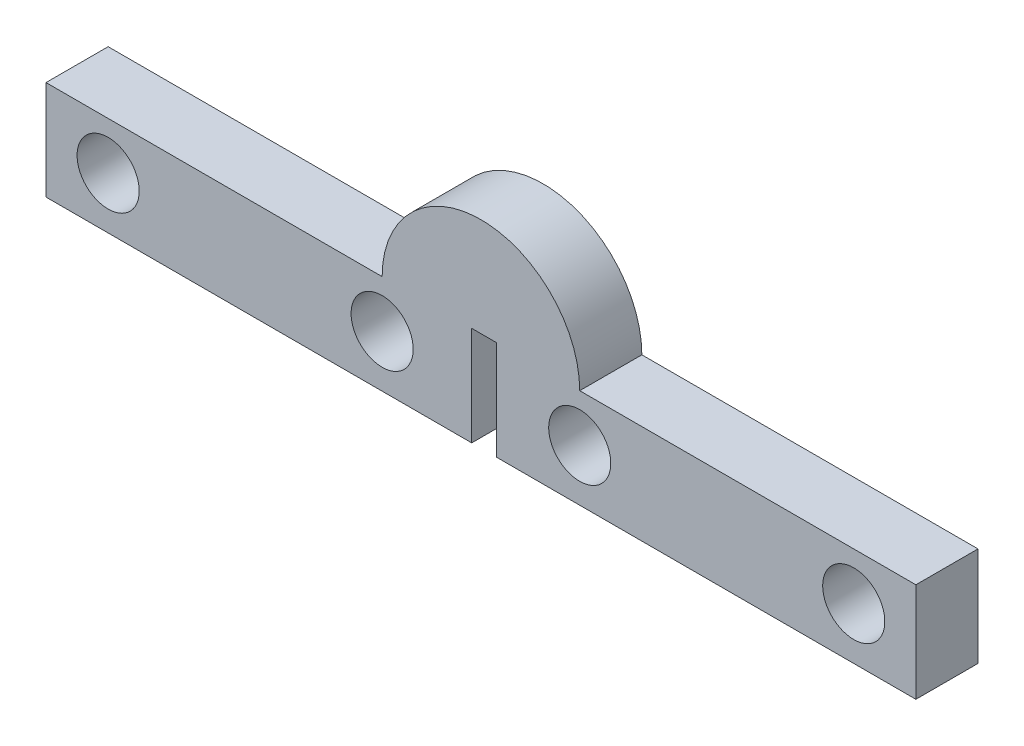
SolidWorks part; units mm, degrees
ref_plane "Front Plane" through (0, 0, 0) normal (0, 0, 1) x (1, 0, 0)
ref_plane "Top Plane" through (0, 0, 0) normal (0, 1, 0) x (1, 0, 0)
ref_plane "Right Plane" through (0, 0, 0) normal (1, 0, 0) x (0, 0, -1)
sketch "Sketch1" plane through (0, 0, 0) normal (0, 0, 1) x (1, 0, 0)
  line L0 (20.555, 4.79) -> (20.555, 0)
  line L1 (0, 0) -> (20.555, 0)
  line L2 (0, 0) -> (0, 4.79)
  line L3 (0, 4.79) -> (16.23, 4.79)
  line L5 (20.555, 4.79) -> (21, 4.79)
  line L6 (21, 9.56) -> (21, 4.79)
  circle A0 centre (3, 2.5) radius 1.5
  circle A1 centre (16.23, 2.5) radius 1.5
  arc A3 (21, 9.56) -> (16.23, 4.79) centre (21, 4.79) ccw
  dimension "D3" = 3
  dimension "D4" = 3
  dimension "D5" = 3
  dimension "D6" = 13.23
  dimension "D2" = 2.29
  dimension "D1" = 4.79
  dimension "D8" = 4.325
extrude "Boss-Extrude1" add sketch "Sketch1" along normal blind 3
mirror "Mirror1" about plane through (21, 9.56, 3) normal (-1, 0, 0) of "Boss-Extrude1"
sketch "Sketch2" plane through (0, 0, 3) normal (0, 0, 1) x (1, 0, 0)
  line L0 (20.555, 4.79) -> (20.555, 0)
  line L7 (20.555, 0) -> (21.745, 0)
  line L9 (20.555, 4.79) -> (21.745, 4.79)
  line L10 (21.745, 0) -> (21.745, 4.79)
  line L12 (21.445, 0) -> (21.445, 4.79) construction
  dimension "D2" = 0.3
extrude "Cut-Extrude1" cut sketch "Sketch2" against normal blind 10
